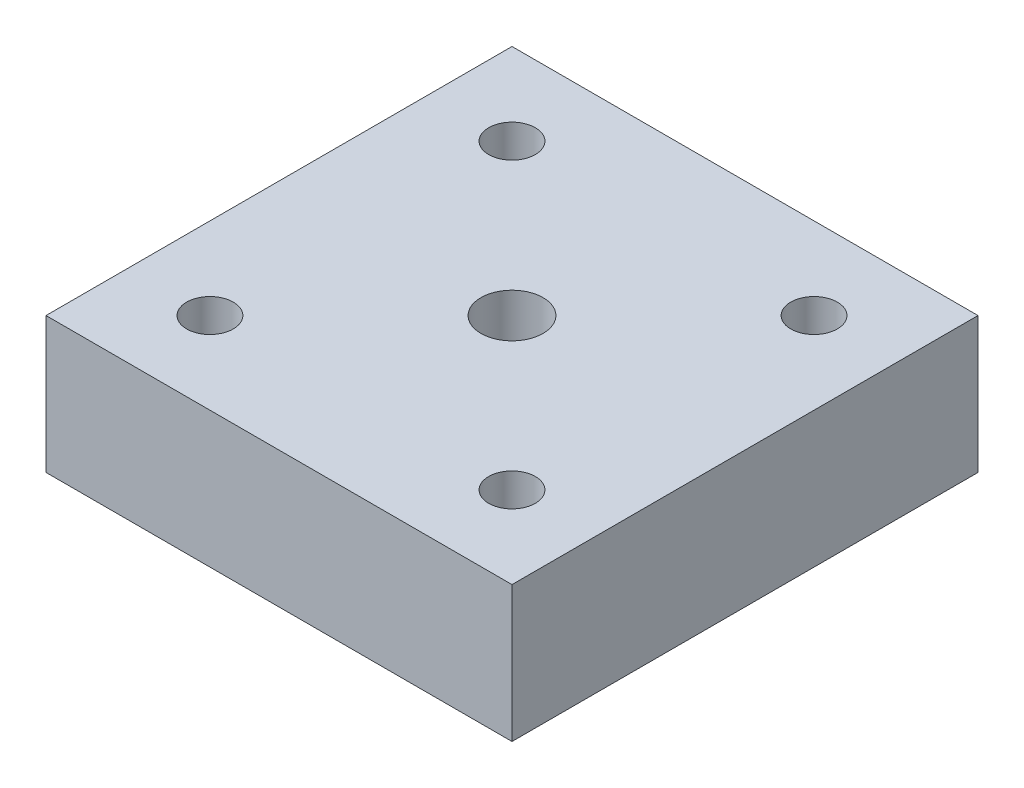
SolidWorks part; units mm, degrees
material "ABS"
ref_plane "Front Plane" through (0, 0, 0) normal (0, 0, 1) x (1, 0, 0)
ref_plane "Top Plane" through (0, 0, 0) normal (0, 1, 0) x (1, 0, 0)
ref_plane "Right Plane" through (0, 0, 0) normal (1, 0, 0) x (0, 0, -1)
sketch "Sketch1" plane through (0, 0, 0) normal (0, 1, 0) x (1, 0, 0)
  line L0 (0, 0) -> (-38.8909, -38.8909) construction
  line L1 (-60, 60) -> (60, 60)
  line L2 (-60, 60) -> (-60, -60)
  line L3 (-60, -60) -> (60, -60)
  line L4 (60, 60) -> (60, -60)
  line L5 (0, 0) -> (-60, -60) construction
  line L6 (38.8909, -38.8909) -> (0, 0) construction
  line L7 (60, -60) -> (0, 0) construction
  line L8 (0, 0) -> (-38.8909, 38.8909) construction
  line L9 (0, 0) -> (-60, 60) construction
  line L10 (38.8909, 38.8909) -> (0, 0) construction
  line L11 (0, 0) -> (60, 60) construction
  circle A0 centre (0, 0) radius 8
  circle A1 centre (-38.8909, -38.8909) radius 6
  circle A2 centre (38.8909, -38.8909) radius 6
  circle A3 centre (-38.8909, 38.8909) radius 6
  circle A4 centre (38.8909, 38.8909) radius 6
  point P16 (-60, 0)
  dimension "D1" = 16
  dimension "D3" = 12
  dimension "D5" = 12
  dimension "D7" = 12
  dimension "D10" = 12
  dimension "D2" = 55
  dimension "D4" = 55
  dimension "D8" = 55
  dimension "D11" = 55
  dimension "D13" = 120
  dimension "D14" = 120
  dimension "D15" = 60
  dimension "D16" = 60
extrude "Boss-Extrude1" add sketch "Sketch1" along normal blind 35
